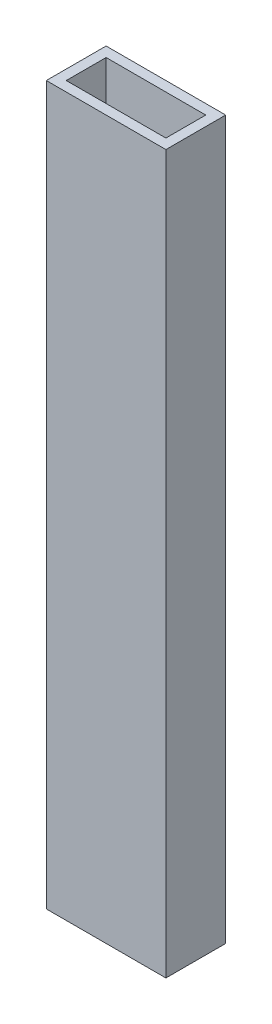
SolidWorks part; units mm, degrees
ref_plane "Front Plane" through (0, 0, 0) normal (0, 0, 1) x (1, 0, 0)
ref_plane "Top Plane" through (0, 0, 0) normal (0, 1, 0) x (1, 0, 0)
ref_plane "Right Plane" through (0, 0, 0) normal (1, 0, 0) x (0, 0, -1)
sketch "Sketch1" plane through (0, 0, 0) normal (0, 1, 0) x (1, 0, 0)
  line L0 (3.175, 15.875) -> (34.925, 15.875)
  line L1 (0, 0) -> (38.1, 0)
  line L2 (0, 0) -> (0, 19.05)
  line L3 (0, 19.05) -> (38.1, 19.05)
  line L4 (38.1, 0) -> (38.1, 19.05)
  line L5 (34.925, 3.175) -> (34.925, 15.875)
  line L6 (3.175, 3.175) -> (34.925, 3.175)
  line L7 (3.175, 3.175) -> (3.175, 15.875)
  dimension "D1" = 38.1
  dimension "D2" = 19.05
extrude "Boss-Extrude1" add sketch "Sketch1" along normal blind 228.6
